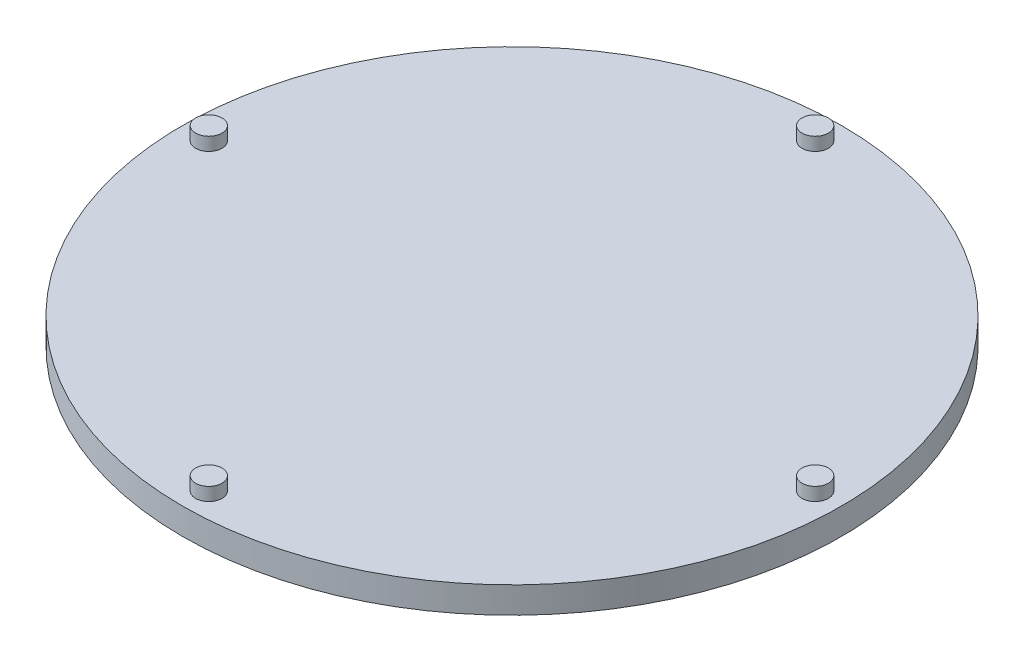
SolidWorks part; units mm, degrees
ref_plane "Front Plane" through (0, 0, 0) normal (0, 0, 1) x (1, 0, 0)
ref_plane "Top Plane" through (0, 0, 0) normal (0, 1, 0) x (1, 0, 0)
ref_plane "Right Plane" through (0, 0, 0) normal (1, 0, 0) x (0, 0, -1)
sketch "Sketch1" plane through (0, 0, 0) normal (0, 1, 0) x (1, 0, 0)
  circle A0 centre (0, 0) radius 25
  dimension "D1" = 50
extrude "Boss-Extrude1" add sketch "Sketch1" along normal blind 2
sketch "Sketch2" plane through (0, 2, 0) normal (0, 1, 0) x (1, 0, 0)
  line L0 (-25, 0) -> (25, 0) construction
  line L1 (0, 25) -> (0, -25) construction
  circle A0 centre (0, 0) radius 25 construction
  circle A1 centre (0, 23) radius 1
  circle A2 centre (23, 0) radius 1
  circle A3 centre (0, -23) radius 1
  circle A4 centre (-23, 0) radius 1
  dimension "D1" = 2
  dimension "D2" = 2
  dimension "D3" = 2
  dimension "D4" = 2
  dimension "D5" = 23
  dimension "D6" = 23
  dimension "D7" = 23
  dimension "D8" = 23
extrude "Boss-Extrude2" add sketch "Sketch2" along normal blind 1
